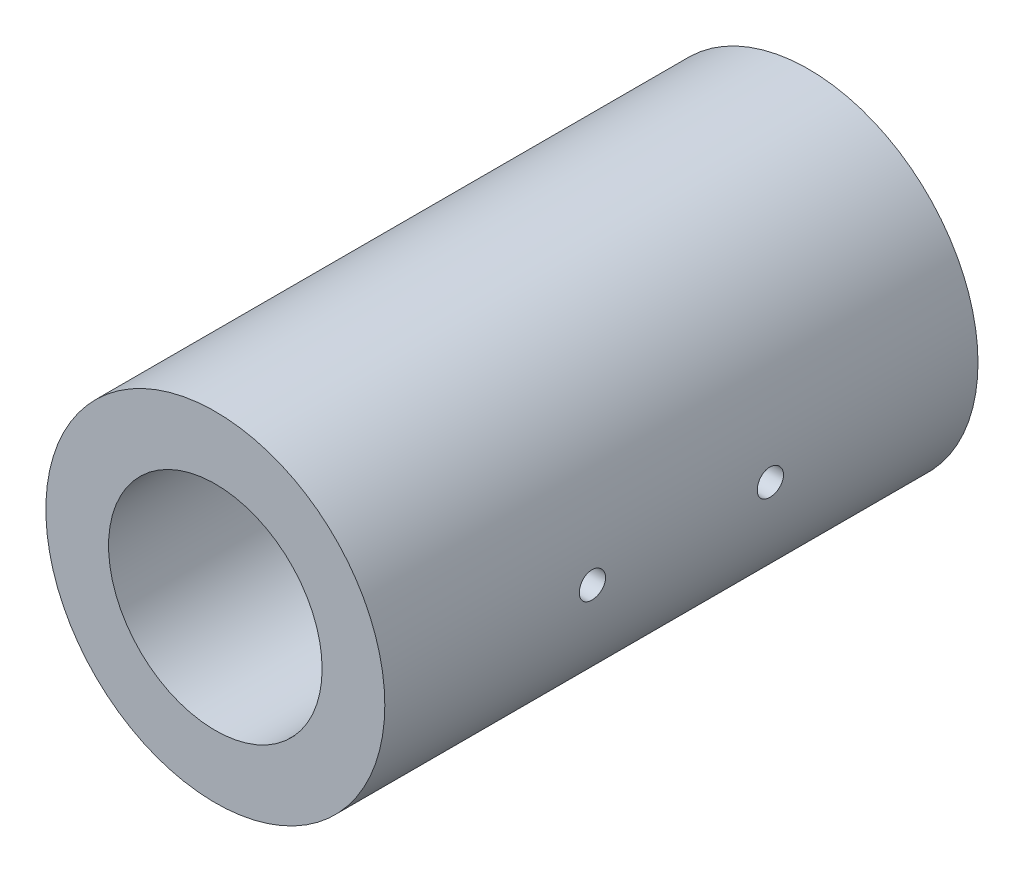
SolidWorks part; units mm, degrees
ref_plane "Front Plane" through (0, 0, 0) normal (0, 0, 1) x (1, 0, 0)
ref_plane "Top Plane" through (0, 0, 0) normal (0, 1, 0) x (1, 0, 0)
ref_plane "Right Plane" through (0, 0, 0) normal (1, 0, 0) x (0, 0, -1)
sketch "Sketch1" plane through (0, 0, 0) normal (0, 0, 1) x (1, 0, 0)
  circle A0 centre (0, 0) radius 20
  circle A1 centre (0, 0) radius 12.6
  dimension "D1" = 40
  dimension "D2" = 25.2
extrude "Boss-Extrude1" add sketch "Sketch1" along normal blind 70
sketch "Sketch2" plane through (0, 0, 0) normal (0, 0, -1) x (-1, 0, 0)
  circle A0 centre (0, 0) radius 15.25
  circle A1 centre (0, 15.25) radius 1.5
  circle A2 centre (15.25, 0) radius 1.5
  circle A3 centre (0, -15.25) radius 1.5
  circle A4 centre (-15.25, 0) radius 1.5
  point P14 (0, 0)
  dimension "D1" = 30.5
  dimension "D2" = 3
  dimension "D3" = 4
extrude "Cut-Extrude1" cut sketch "Sketch2" against normal blind 10 contours A4 | A3 | A2 | A1
sketch "Sketch3" plane through (0, 0, 0) normal (1, 0, 0) x (0, 0, -1)
  line L0 (-35, 20) -> (-35, 0) construction
  line L1 (0, 20) -> (-70, 20) construction
  line L2 (-35, 0) -> (-24.5, 0) construction
  line L3 (-35, 0) -> (-45.5, 0) construction
  circle A0 centre (-45.5, 0) radius 1.55
  circle A1 centre (-24.5, 0) radius 1.55
  dimension "D3" = 3.1
  dimension "D4" = 3.1
  dimension "D1" = 10.5
  dimension "D2" = 10.5
extrude "Cut-Extrude2" cut sketch "Sketch3" against normal through all both and the other way through all
